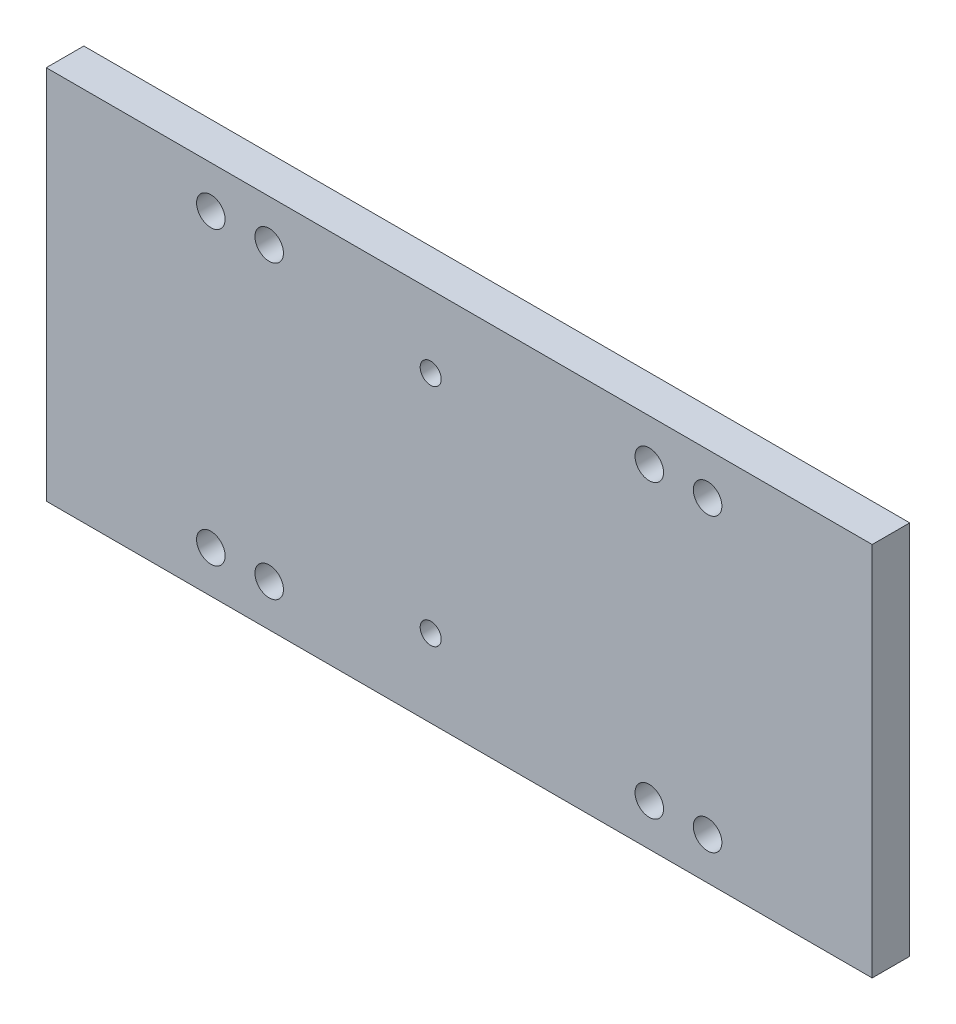
SolidWorks part; units mm, degrees
ref_plane "Front Plane" through (0, 0, 0) normal (0, 0, 1) x (1, 0, 0)
ref_plane "Top Plane" through (0, 0, 0) normal (0, 1, 0) x (1, 0, 0)
ref_plane "Right Plane" through (0, 0, 0) normal (1, 0, 0) x (0, 0, -1)
sketch "Sketch1" plane through (0, 0, 0) normal (0, 0, 1) x (1, 0, 0)
  line L1 (0, 0) -> (139.7, 0)
  line L2 (0, 0) -> (0, 63.5)
  line L3 (0, 63.5) -> (139.7, 63.5)
  line L4 (139.7, 0) -> (139.7, 63.5)
  dimension "D1" = 139.7
  dimension "D2" = 63.5
extrude "Boss-Extrude1" add sketch "Sketch1" along normal blind 6.35
sketch "Sketch2" plane through (0, 0, 0) normal (0, 0, -1) x (-1, 0, 0)
  circle A0 centre (-65.024, 13.1578) radius 1.778
  circle A1 centre (-65.024, 51.2578) radius 1.778
extrude "Cut-Extrude1" cut sketch "Sketch2" against normal up to surface (6.35 mm away) contours A0 | A1 up to face at (69.85, 31.75, 6.35)
sketch "Sketch3" plane through (0, 0, 0) normal (0, 0, -1) x (-1, 0, 0)
  circle A0 centre (-111.865, 7.1) radius 2.413
  circle A1 centre (-101.995, 7.1) radius 2.413
  circle A2 centre (-111.865, 56.4) radius 2.413
  circle A3 centre (-101.995, 56.4) radius 2.413
  circle A4 centre (-37.705, 56.4) radius 2.413
  circle A5 centre (-27.835, 56.4) radius 2.413
  circle A6 centre (-27.835, 7.1) radius 2.413
  circle A7 centre (-37.705, 7.1) radius 2.413
  dimension "D1" = 4.826
  dimension "D2" = 4.826
  dimension "D3" = 4.826
  dimension "D4" = 4.826
  dimension "D5" = 4.826
  dimension "D6" = 4.826
  dimension "D7" = 4.826
  dimension "D8" = 4.826
extrude "Cut-Extrude2" cut sketch "Sketch3" against normal up to surface (6.35 mm away) up to face at (63.246, 13.1578, 6.35)
